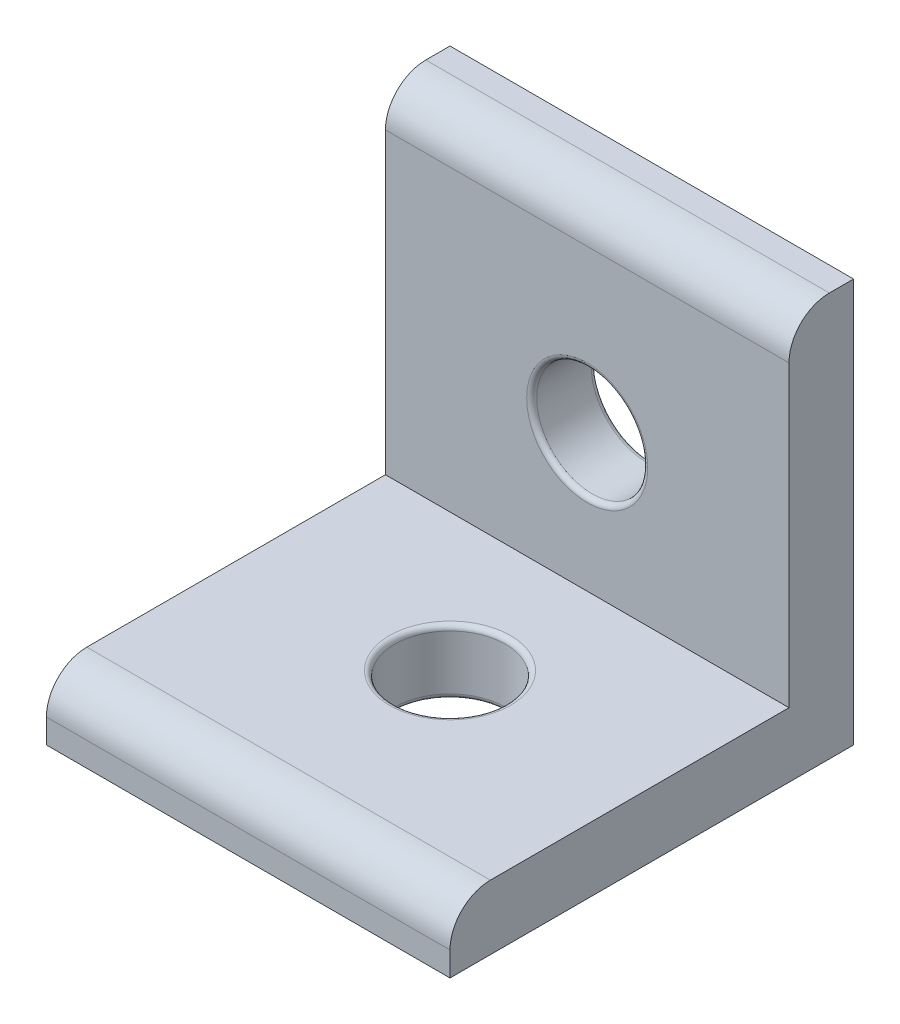
SolidWorks part; units mm, degrees
ref_plane "Front Plane" through (0, 0, 0) normal (0, 0, 1) x (1, 0, 0)
ref_plane "Top Plane" through (0, 0, 0) normal (0, 1, 0) x (1, 0, 0)
ref_plane "Right Plane" through (0, 0, 0) normal (1, 0, 0) x (0, 0, -1)
sketch "Sketch1" plane through (0, 0, 0) normal (0, 1, 0) x (1, 0, 0)
  line L1 (-10, -10) -> (10, -10)
  line L2 (-10, -10) -> (-10, 10)
  line L3 (-10, 10) -> (10, 10)
  line L4 (10, -10) -> (10, 10)
  line L5 (-10, -10) -> (10, 10) construction
  line L6 (-10, 10) -> (10, -10) construction
  point P0 (0, 0)
  dimension "D1" = 20
  dimension "D2" = 20
extrude "Boss-Extrude1" add sketch "Sketch1" along normal blind 3.2
sketch "Sketch2" plane through (0, 3.2, 0) normal (0, 1, 0) x (1, 0, 0)
  line L0 (10, -10) -> (10, 10) construction
  line L1 (-10, 10) -> (10, 10)
  line L2 (-10, 10) -> (-10, 6.8)
  line L3 (-10, 6.8) -> (10, 6.8)
  line L4 (10, 10) -> (10, 6.8)
  dimension "D1" = 3.2
extrude "Boss-Extrude2" add sketch "Sketch2" along normal blind 16.8
sketch "Sketch3" plane through (0, 3.2, 0) normal (0, 1, 0) x (1, 0, 0)
  circle A0 centre (0, 0) radius 2.75
  dimension "D1" = 5.5
extrude "Cut-Extrude1" cut sketch "Sketch3" against normal through all
sketch "Sketch4" plane through (0, 0, -6.8) normal (0, 0, 1) x (1, 0, 0)
  circle A0 centre (0, 10) radius 2.75
  dimension "D2" = 5.5
  dimension "D1" = 10
extrude "Cut-Extrude2" cut sketch "Sketch4" against normal through all
fillet "Fillet1" radius 2 2 edges at (0, 20, -6.8) (0, 3.2, 10)
fillet "Fillet2" radius 0.25 4 edges at (2.75, 10, -6.8) (2.75, 10, -10) (0, 3.2, 2.75) (0, 0, 2.75)
